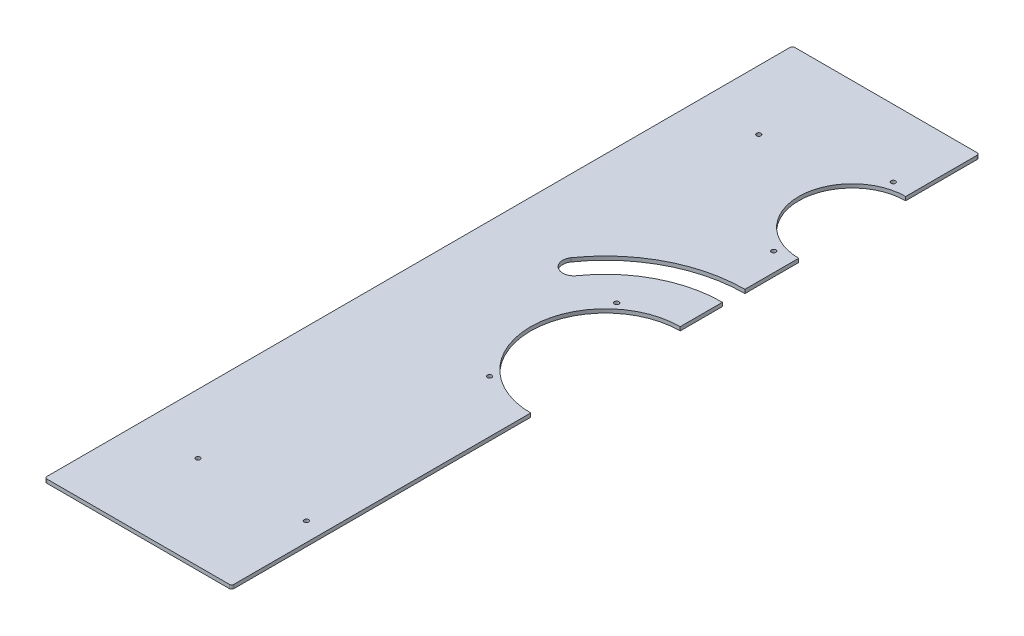
SolidWorks part; units mm, degrees
material "AISI 1045 Steel, cold drawn"
ref_plane "Front Plane" through (0, 0, 0) normal (0, 0, 1) x (1, 0, 0)
ref_plane "Top Plane" through (0, 0, 0) normal (0, 1, 0) x (1, 0, 0)
ref_plane "Right Plane" through (0, 0, 0) normal (1, 0, 0) x (0, 0, -1)
sketch "Sketch1" plane through (0, 0, 0) normal (0, 1, 0) x (1, 0, 0)
  line L1 (-125, -500) -> (125, -500)
  line L2 (-125, -500) -> (-125, 500)
  line L3 (-125, 500) -> (125, 500)
  line L4 (125, -500) -> (125, 500)
  line L5 (-125, -500) -> (125, 500) construction
  line L6 (-125, 500) -> (125, -500) construction
  point P0 (0, 0)
  dimension "D1" = 250
  dimension "D2" = 1000
extrude "Boss-Extrude1" add sketch "Sketch1" along normal blind 5
fillet "Fillet1" radius 3 4 edges at (-125, 2.5, 500) (-125, 2.5, -500) (125, 2.5, -500) (125, 2.5, 500)
sketch "Sketch3" plane through (0, 5, 0) normal (0, 1, 0) x (1, 0, 0)
  line L0 (125, -497) -> (125, 497) construction
  line L1 (-122, -500) -> (122, -500) construction
  line L2 (-125, 497) -> (-125, -497) construction
  line L3 (-125, 0) -> (0, 0) construction
  line L4 (-15.4846, 98.3684) -> (125, 0) construction
  line L5 (125, 171.5) -> (125, 0) construction
  line L10 (125, 0) -> (-0.4272, 116.9627) construction
  line L11 (24.984, 128.8169) -> (-10.4799, 90.7865) construction
  line L12 (24.984, 128.8169) -> (9.6256, 143.1389) construction
  line L13 (-10.4799, 90.7865) -> (-25.8383, 105.1085) construction
  line L14 (9.6256, 143.1389) -> (-25.8383, 105.1085) construction
  line L15 (24.984, 128.8169) -> (-25.8383, 105.1085) construction
  line L16 (-10.4799, 90.7865) -> (9.6256, 143.1389) construction
  line L17 (-0.4272, 116.9627) -> (7.2658, 125.2124) construction
  line L18 (125, 330) -> (16.0035, 330) construction
  circle A0 centre (125, 330) radius 71.5
  circle A1 centre (125, 0) radius 100
  circle A2 centre (-45, -375) radius 3
  circle A3 centre (-45, 375) radius 3
  circle A4 centre (55, -85) radius 3
  circle A6 centre (55, 85) radius 3
  arc A7 (125, 171.5) -> (-15.4846, 98.3684) centre (125, 0) ccw construction
  arc A8 (125, 186.5) -> (-27.7719, 106.972) centre (125, 0) ccw
  arc A9 (125, 156.5) -> (-3.1973, 89.7647) centre (125, 0) ccw
  arc A10 (125, 186.5) -> (125, 156.5) centre (125, 171.5) cw
  arc A11 (-27.7719, 106.972) -> (-3.1973, 89.7647) centre (-15.4846, 98.3684) ccw
  circle A12 centre (100, 410) radius 3
  circle A13 centre (100, 250) radius 3
  circle A14 centre (100, -375) radius 3
  dimension "D1" = 143
  dimension "D3" = 200
  dimension "D4" = 125
  dimension "D5" = 80
  dimension "D6" = 6
  dimension "D7" = 70
  dimension "D8" = 85
  dimension "D13" = 25
  dimension "D17" = 80
  dimension "D18" = 25
  dimension "D2" = 330
  dimension "D9" = 171.5
  dimension "D10" = 55
  dimension "D14" = 47
  dimension "D15" = 52
  dimension "D16" = 21
  dimension "D11" = 15
  dimension "D12" = 15
extrude "Cut-Extrude2" cut sketch "Sketch3" against normal up to next
